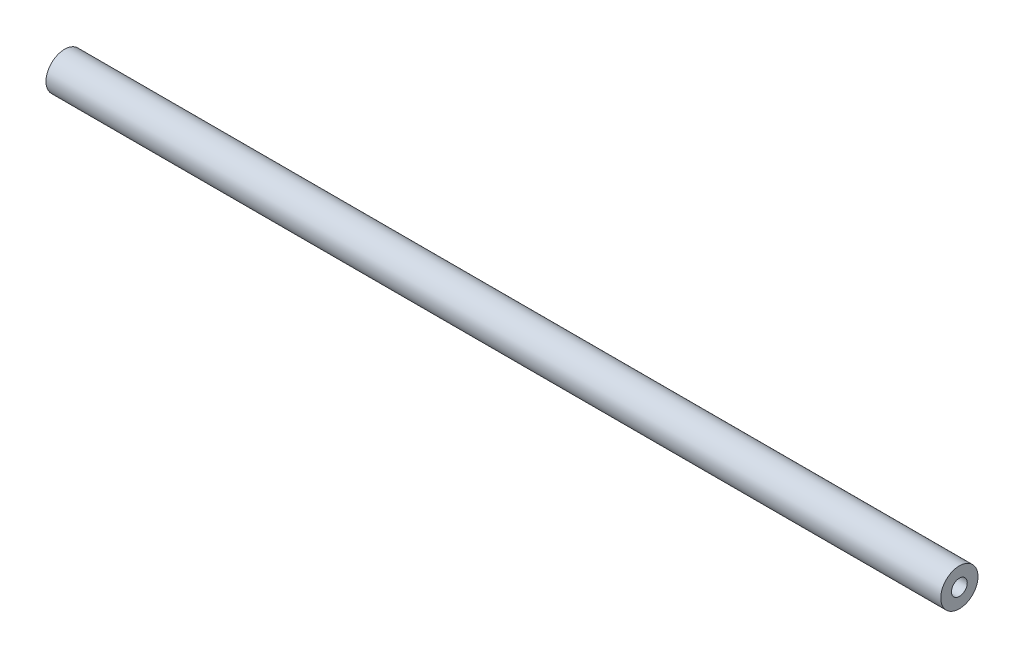
SolidWorks part; units mm, degrees
material "6061 Alloy"
ref_plane "Front Plane" through (0, 0, 0) normal (0, 0, 1) x (1, 0, 0)
ref_plane "Top Plane" through (0, 0, 0) normal (0, 1, 0) x (1, 0, 0)
ref_plane "Right Plane" through (0, 0, 0) normal (1, 0, 0) x (0, 0, -1)
sketch "Sketch1" plane through (0, 0, 0) normal (1, 0, 0) x (0, 0, -1)
  circle A0 centre (0, 0) radius 4.7625
  dimension "D1" = 9.525
extrude "Boss-Extrude1" add sketch "Sketch1" along normal mid plane 228.6
hole_wizard "#10-32 Tapped Hole1" positions "Sketch3" profile "Sketch2" tap size "#10-32" standard "ANSI Inch"
sketch "Sketch3" plane through (-114.3, 0, 0) normal (-1, 0, 0) x (0, 0, 1)
  point P0 (0, 0)
sketch "Sketch2" plane through (-114.3, 0, 0) normal (0, 1, 0) x (0, 0, 1)
  line L0 (0, 0) -> (0, 11.938)
  line L1 (0, 11.938) -> (2.0193, 11.938)
  line L2 (2.0193, 11.938) -> (2.0193, 0)
  line L5 (2.0193, 0) -> (0, 0)
  line L10 (0, 11.938) -> (-2.0193, 11.938) construction
  line L11 (0, -6.35) -> (0, 107.95) construction
  dimension "Tap Drill Dia." = 4.0386
  dimension "Tap Drill Depth" = 11.938
  dimension "Drill Angle" = 180
cosmetic thread "Hole Thread1" parameters "D1"=9.652, "D2"=4.826
mirror "Mirror1" about plane through (0, 0, 0) normal (1, 0, 0) of "#10-32 Tapped Hole1"
